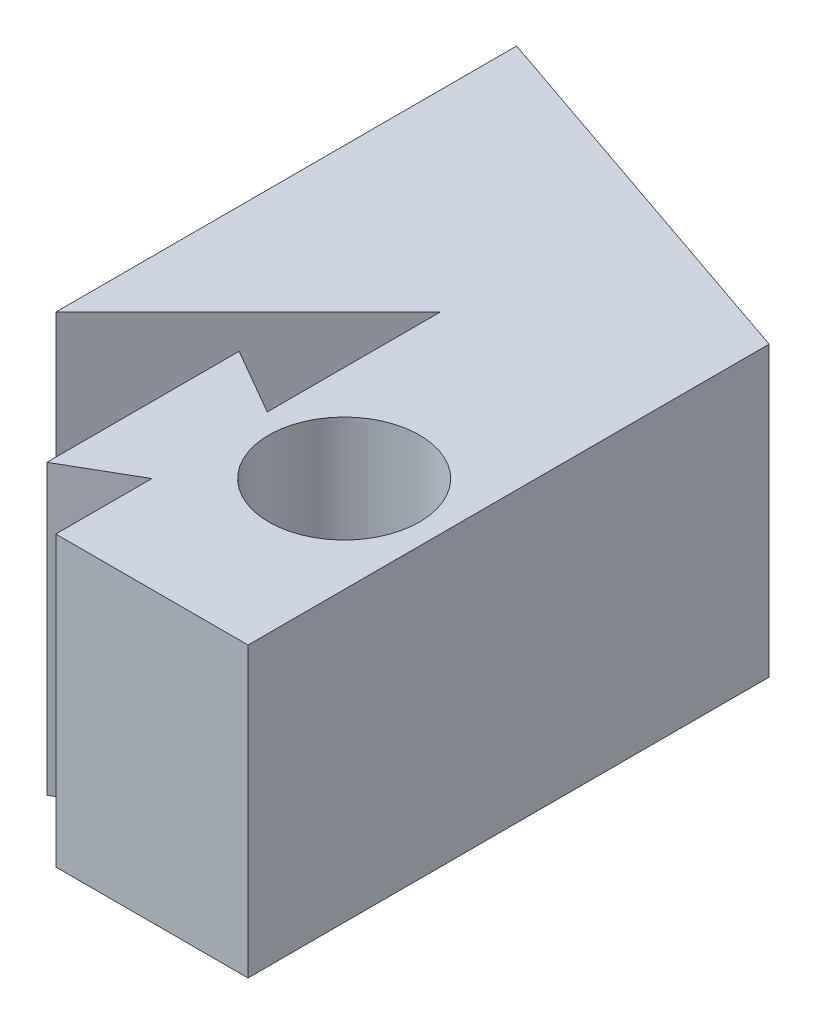
SolidWorks part; units mm, degrees
material "PE High Density"
ref_plane "Front Plane" through (0, 0, 0) normal (0, 0, 1) x (1, 0, 0)
ref_plane "Top Plane" through (0, 0, 0) normal (0, 1, 0) x (1, 0, 0)
ref_plane "Right Plane" through (0, 0, 0) normal (1, 0, 0) x (0, 0, -1)
sketch "Sketch2" plane through (0, 0, 0) normal (0, 1, 0) x (1, 0, 0)
  line L0 (0, 0) -> (-3.175, 0) construction
  line L1 (0, 0) -> (0, 9.525) construction
  line L2 (-3.175, 6.35) -> (-3.175, 12.7)
  line L3 (-3.175, 12.7) -> (9.525, 12.7)
  line L4 (3.175, 6.985) -> (3.175, 12.7)
  line L5 (0.9753, 8.255) -> (3.175, 6.985)
  line L6 (0.9753, 8.255) -> (0.9753, 1.905)
  line L7 (3.175, 3.175) -> (3.175, 0)
  line L8 (3.175, 0) -> (9.525, 0)
  line L9 (9.525, 0) -> (9.525, 12.7)
  line L10 (3.175, 12.7) -> (3.175, 6.985)
  line L11 (0.9753, 8.255) -> (0.9753, 1.905)
  line L12 (3.175, 3.175) -> (0.9753, 1.905)
  line L13 (3.175, 3.175) -> (3.175, 0)
  line L14 (3.175, 0) -> (3.175, 12.7)
  circle A0 centre (6.35, 6.35) radius 2.4892
  line B0 (-3.175, 6.35) -> (-3.175, 0)
  line B1 (-3.175, 0) -> (3.175, 0)
  line B2 (3.175, 0) -> (3.175, 3.175)
  line B3 (3.175, 3.175) -> (0.9753, 1.905)
  line B4 (0.9753, 1.905) -> (0.9753, 8.255)
  line B5 (0.9753, 8.255) -> (3.175, 6.985)
  line B6 (3.175, 6.985) -> (3.175, 12.7)
  line B7 (3.175, 12.7) -> (-3.175, 6.35)
  dimension "D3" = 4.9784
  dimension "D1" = 3.175
  dimension "D2" = 12.7
  dimension "D4" = 6.35
  dimension "D5" = 3.175
sketch_block_instance "Forks-1"
sketch_block "Forks"
extrude "Boss-Extrude3" add sketch "Sketch2" along normal blind 9.525 contours A0
sketch "Sketch3" plane through (0, 9.525, 0) normal (0, 1, 0) x (1, 0, 0)
  line L0 (-3.175, 6.35) -> (-3.175, 12.7)
  line L1 (-3.175, 12.7) -> (9.525, 12.7)
  line L2 (9.525, 12.7) -> (9.525, 0)
  line L3 (9.525, 0) -> (-3.175, 0)
  line L4 (-3.175, 0) -> (-3.175, 6.35)
  line L5 (-3.175, 6.35) -> (3.175, 12.7)
  line L6 (3.175, 12.7) -> (3.175, 6.985)
  line L7 (3.175, 6.985) -> (0.9753, 8.255)
  line L8 (0.9753, 8.255) -> (0.9753, 1.905)
  line L9 (0.9753, 1.905) -> (3.175, 3.175)
  line L10 (3.175, 3.175) -> (3.175, 0)
  circle M1 centre (6.35, 6.35) radius 2.4892
extrude "Boss-Extrude4" add sketch "Sketch3" against normal up to surface (9.525 mm away) contours L9 L10 L3 L2 L1 L6 L7 L8 M1 | L0 L5 L1 up to face at (6.35, 0, -3.8608)
sketch "Sketch4" plane through (0, 9.525, 0) normal (0, 1, 0) x (1, 0, 0)
  line L0 (9.525, 0) -> (9.525, 12.7) construction
  line L1 (-3.175, 12.7) -> (9.525, 12.7)
  line L2 (-3.175, 12.7) -> (-3.175, 13.97)
  line L3 (-3.175, 13.97) -> (9.525, 13.97)
  line L4 (9.525, 12.7) -> (9.525, 13.97)
  dimension "D1" = 1.27
extrude "Boss-Extrude5" add sketch "Sketch4" against normal up to surface (9.525 mm away) up to face at (4.2126, 0, -5.715)
sketch "Sketch5" plane through (0, 9.525, 0) normal (0, 1, 0) x (1, 0, 0)
  circle A0 centre (6.35, 6.35) radius 2.4892
extrude "Cut-Extrude1" cut sketch "Sketch5" against normal through all both and the other way through all
sketch "Sketch7" plane through (0, 9.525, 0) normal (0, 1, 0) x (1, 0, 0)
  line L0 (9.525, 13.97) -> (-3.175, 13.97) construction
  line B0 (9.525, 13.97) -> (9.525, 17.2125)
  line B1 (9.525, 17.2125) -> (-3.175, 21.5712)
  line B2 (-3.175, 21.5712) -> (-3.175, 13.97)
  line B3 (-3.175, 13.97) -> (9.525, 13.97)
sketch_block_instance "other mount for thing-3"
sketch_block "other mount for thing"
extrude "Boss-Extrude7" add sketch "Sketch7" against normal up to surface (9.525 mm away) up to face at (6.35, 0, -3.8608)
